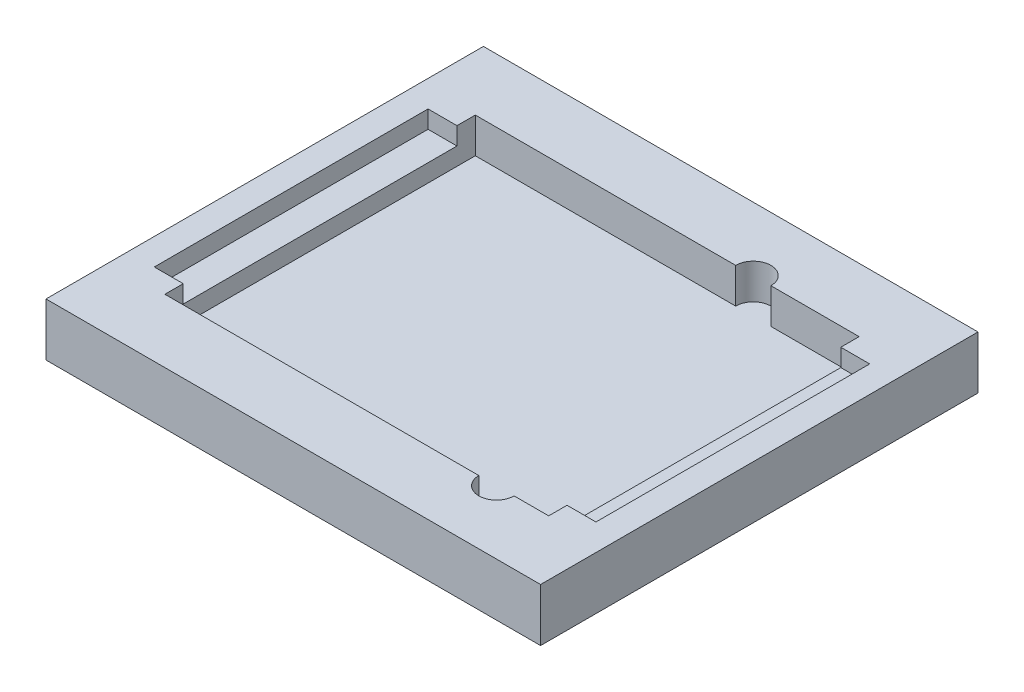
SolidWorks part; units mm, degrees
ref_plane "Front Plane" through (0, 0, 0) normal (0, 0, 1) x (1, 0, 0)
ref_plane "Top Plane" through (0, 0, 0) normal (0, 1, 0) x (1, 0, 0)
ref_plane "Right Plane" through (0, 0, 0) normal (1, 0, 0) x (0, 0, -1)
sketch "Sketch1" plane through (0, 0, 0) normal (0, 1, 0) x (1, 0, 0)
  line L1 (2.54, 0) -> (80.01, 0)
  line L2 (0, 2.54) -> (0, 69.596)
  line L3 (2.54, 72.136) -> (80.01, 72.136)
  line L4 (82.55, 2.54) -> (82.55, 69.596)
  arc A0 (2.54, 0) -> (0, 2.54) centre (2.54, 2.54) cw
  arc A1 (80.01, 0) -> (82.55, 2.54) centre (80.01, 2.54) ccw
  arc A2 (80.01, 72.136) -> (82.55, 69.596) centre (80.01, 69.596) cw
  arc A3 (2.54, 72.136) -> (0, 69.596) centre (2.54, 69.596) ccw
  point P7 (0, 0)
  point P10 (82.55, 0)
  point P15 (0, 72.136)
  dimension "D3" = 2.54
  dimension "D1" = 72.136
  dimension "D2" = 82.55
extrude "Boss-Extrude1" add sketch "Sketch1" along normal blind 3.175
sketch "Sketch2" plane through (0, 3.175, 0) normal (0, 1, 0) x (1, 0, 0)
  line L0 (0, 36.068) -> (-3.2385, 36.068) construction
  line L1 (85.7885, 75.438) -> (-3.2385, 75.438)
  line L2 (85.7885, 75.438) -> (85.7885, -3.302)
  line L3 (85.7885, -3.302) -> (-3.2385, -3.302)
  line L4 (-3.2385, 75.438) -> (-3.2385, -3.302)
  line L5 (0, 69.596) -> (0, 2.54) construction
  line L6 (41.275, 75.438) -> (41.275, 72.136) construction
  line L7 (80.01, 72.136) -> (2.54, 72.136) construction
  dimension "D1" = 89.027
  dimension "D2" = 78.74
extrude "Boss-Extrude2" add sketch "Sketch2" along normal blind 6.35 contours L2 L3 L4 L1
sketch "Sketch3" plane through (0, 9.525, 0) normal (0, 1, 0) x (1, 0, 0)
  line L0 (41.275, 36.068) -> (-3.2385, 36.068) construction
  line L1 (6.731, 8.128) -> (63.246, 8.128)
  line L2 (6.731, 8.128) -> (6.731, 64.008)
  line L3 (6.731, 64.008) -> (53.594, 64.008)
  line L4 (75.819, 8.128) -> (75.819, 64.008)
  line L5 (6.731, 8.128) -> (75.819, 64.008) construction
  line L6 (6.731, 64.008) -> (75.819, 8.128) construction
  line L7 (-3.2385, 75.438) -> (-3.2385, -3.302) construction
  line L8 (41.275, 36.068) -> (41.275, 75.438) construction
  line L9 (85.7885, 75.438) -> (-3.2385, 75.438) construction
  line L10 (59.944, 64.008) -> (75.819, 64.008)
  line L11 (69.596, 8.128) -> (75.819, 8.128)
  arc A0 (59.944, 64.008) -> (53.594, 64.008) centre (56.769, 64.008) ccw
  arc A1 (63.246, 8.128) -> (69.596, 8.128) centre (66.421, 8.128) ccw
  point P0 (41.275, 36.068)
  dimension "D5" = 6.35
  dimension "D6" = 6.35
  dimension "D1" = 55.88
  dimension "D2" = 69.088
  dimension "D3" = 9.398
  dimension "D4" = 19.05
extrude "Cut-Extrude1" cut sketch "Sketch3" against normal blind 3.175 contours L3 A0 L10 L4 L11 A1 L1 L2
sketch "Sketch4" plane through (0, 9.525, 0) normal (0, 1, 0) x (1, 0, 0)
  line L0 (-3.2385, 75.438) -> (-3.2385, -3.302) construction
  line L1 (85.7885, 75.438) -> (-3.2385, 75.438)
  line L2 (85.7885, 75.438) -> (85.7885, -3.302)
  line L3 (85.7885, -3.302) -> (-3.2385, -3.302)
  line L4 (-3.2385, 75.438) -> (-3.2385, -3.302)
  line L5 (41.275, 36.068) -> (-3.2385, 36.068) construction
  line L6 (1.524, 11.43) -> (6.731, 11.43)
  line L7 (1.524, 11.43) -> (1.524, 60.706)
  line L8 (1.524, 60.706) -> (6.731, 60.706)
  line L9 (81.026, 11.43) -> (81.026, 60.706)
  line L10 (1.524, 11.43) -> (81.026, 60.706) construction
  line L11 (1.524, 60.706) -> (81.026, 11.43) construction
  line L12 (41.275, 36.068) -> (41.275, 75.438) construction
  line L13 (85.7885, -3.302) -> (-3.2385, -3.302) construction
  line L14 (75.819, 8.128) -> (75.819, 64.008) construction
  line L15 (81.026, 60.706) -> (75.819, 60.706)
  line L16 (81.026, 60.706) -> (81.026, 11.43)
  line L17 (81.026, 11.43) -> (75.819, 11.43)
  line L19 (6.731, 8.128) -> (6.731, 64.008) construction
  line L20 (1.524, 11.43) -> (6.731, 11.43)
  line L21 (1.524, 11.43) -> (1.524, 60.706)
  line L22 (1.524, 60.706) -> (6.731, 60.706)
  line L24 (75.819, 60.706) -> (81.026, 60.706)
  line L25 (75.819, 11.43) -> (81.026, 11.43)
  line L26 (6.731, 60.706) -> (6.731, 64.008)
  line L27 (6.731, 64.008) -> (53.594, 64.008)
  line L28 (6.731, 64.008) -> (53.594, 64.008) construction
  line L29 (59.944, 64.008) -> (75.819, 64.008) construction
  line L30 (59.944, 64.008) -> (75.819, 64.008)
  line L31 (75.819, 64.008) -> (75.819, 60.706)
  line L32 (75.819, 11.43) -> (75.819, 8.128)
  line L33 (75.819, 8.128) -> (69.596, 8.128)
  line L34 (69.596, 8.128) -> (75.819, 8.128) construction
  line L35 (63.246, 8.128) -> (6.731, 8.128)
  line L36 (6.731, 8.128) -> (6.731, 11.43)
  arc A0 (59.944, 64.008) -> (53.594, 64.008) centre (56.769, 64.008) ccw construction
  arc A1 (53.594, 64.008) -> (59.944, 64.008) centre (56.769, 64.008) cw
  arc A2 (69.596, 8.128) -> (63.246, 8.128) centre (66.421, 8.128) cw
  arc A3 (63.246, 8.128) -> (69.596, 8.128) centre (66.421, 8.128) ccw construction
  point P7 (41.275, 36.068)
  line M19 (85.7885, 75.438) -> (-3.2385, 75.438)
  line M20 (-3.2385, 75.438) -> (-3.2385, -3.302)
  line M21 (-3.2385, -3.302) -> (85.7885, -3.302)
  line M22 (85.7885, -3.302) -> (85.7885, 75.438)
  line M23 (63.246, 8.128) -> (6.731, 8.128)
  line M24 (6.731, 8.128) -> (6.731, 64.008)
  line M25 (6.731, 64.008) -> (53.594, 64.008)
  arc M26 (53.594, 64.008) -> (59.944, 64.008) centre (56.769, 64.008) cw
  line M27 (59.944, 64.008) -> (75.819, 64.008)
  line M28 (75.819, 64.008) -> (75.819, 8.128)
  line M29 (75.819, 8.128) -> (69.596, 8.128)
  arc M30 (69.596, 8.128) -> (63.246, 8.128) centre (66.421, 8.128) cw
  dimension "D1" = 79.502
  dimension "D2" = 49.276
extrude "Boss-Extrude3" add sketch "Sketch4" along normal blind 3.175 contours L9 L17 L6 L7 L8 L15 M22 M19 M20 M21 M28 M29 M30 M23 M24 M25 M26 M27
